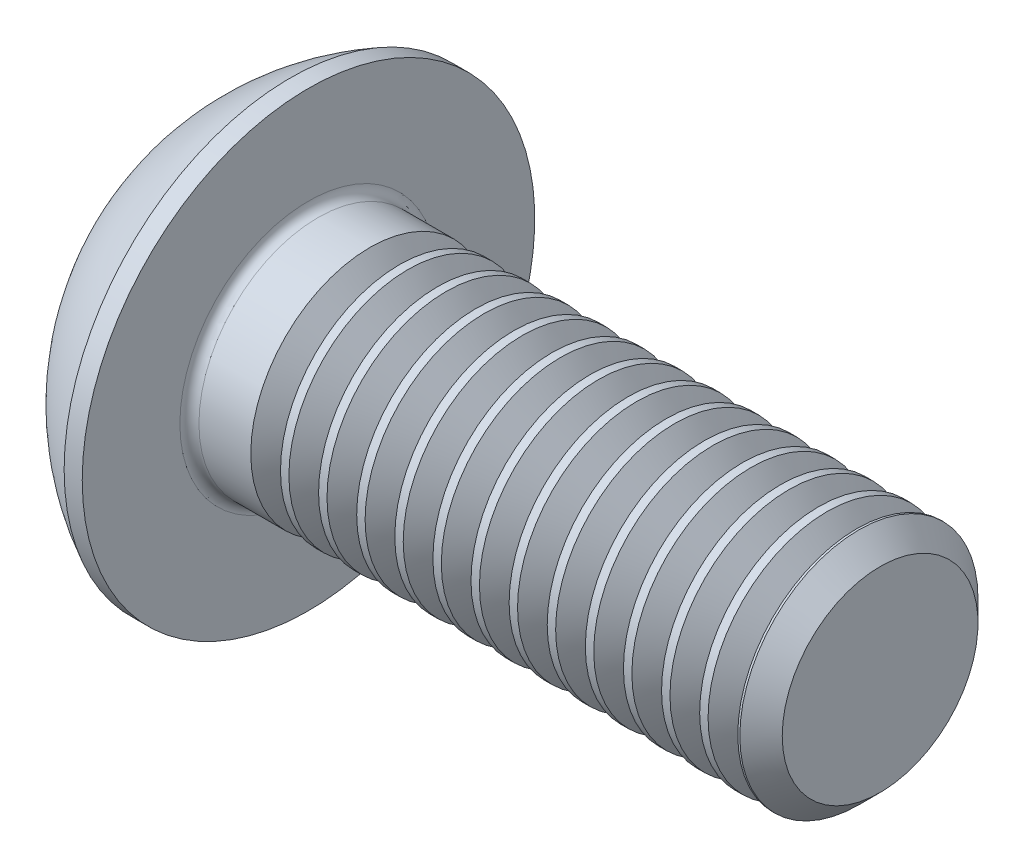
SolidWorks part; units mm, degrees
ref_plane "Plane1" through (0, 0, 0) normal (0, 0, 1) x (1, 0, 0)
ref_plane "Plane2" through (0, 0, 0) normal (0, 1, 0) x (1, 0, 0)
ref_plane "Plane3" through (0, 0, 0) normal (1, 0, 0) x (0, 0, -1)
sketch "BodySke" plane through (0, 0, 0) normal (0, 0, 1) x (1, 0, 0)
  line L0 (14.75, 0) -> (14.75, 2.055)
  line L1 (14.305, 2.5) -> (2.75, 2.5)
  line L2 (2.75, 2.5) -> (2.75, 4.75)
  line L3 (2.75, 4.75) -> (2.37, 4.75)
  line L4 (0, 0) -> (101.6, 0) construction
  line L5 (2.75, -4.75) -> (2.37, -4.75) construction
  line L6 (55.6768, -2.5) -> (2.75, -2.5) construction
  line L7 (14.75, 0) -> (0, 0)
  line L8 (0, 2.375) -> (0, -2.375) construction
  line L9 (0, 0) -> (0, 2.375)
  line L10 (14.75, 2.055) -> (14.305, 2.5)
  line L11 (14.75, -2.055) -> (14.305, -2.5) construction
  line L12 (3.55, 9.525) -> (3.55, -2.5) construction
  line L13 (2.75, 9.525) -> (2.75, -2.5) construction
  arc A1 (0, 2.375) -> (2.37, 4.75) centre (4.755, 0) cw
  dimension "D1" = 4.75
  dimension "Diameter" = 5
  dimension "Length" = 12
  dimension "Head_dia" = 9.5
  dimension "Head_ht" = 2.75
  dimension "Head_side_ht" = 0.38
  dimension "Minor_dia" = 4.11
  dimension "Body_ch_ang" = 45
  dimension "Advance" = 0.8
  dimension "Thread_nom" = 12
revolve "BaseBody" add sketch "BodySke" angle 360 about L4
cosmetic thread "ThreadCosmetic" [suppressed] parameters "Thread_length"=10.4, "Thread_minor"=4.11
fillet "Fillet1" radius 0.2 1 edges at (2.75, 0, 2.5)
sketch "Sketch2" plane through (0, 0, 0) normal (0, 0, 1) x (1, 0, 0)
  line L0 (0, 1.5) -> (1.56, 1.5)
  line L1 (1.56, 1.5) -> (2.426, 0)
  line L3 (2.426, 0) -> (0, 0)
  line L4 (0, 0) -> (0, 1.5)
  line L5 (0, -1.5) -> (1.56, -1.5) construction
  line L6 (0, 0) -> (47.625, 0) construction
  dimension "D2" = 60
  dimension "PreBroach_depth" = 1.56
  dimension "PreBroach_dia" = 3
revolve "PreBroach" cut sketch "Sketch2" angle 360 about L6
sketch "Sketch3" plane through (0, 0, 0) normal (1, 0, 0) x (0, 0, -1)
  line L0 (-1.5, -0.866) -> (-1.5, 0.866)
  line L1 (-1.5, 0.866) -> (0, 1.7321)
  line L2 (0, 1.7321) -> (1.5, 0.866)
  line L3 (1.5, 0.866) -> (1.5, -0.866)
  line L4 (1.5, -0.866) -> (0, -1.7321)
  line L5 (0, -1.7321) -> (-1.5, -0.866)
  dimension "D1" = 1.5
  dimension "D2" = 1.5
  dimension "D3" = 3
  dimension "Hex_size" = 3
extrude "Hex" cut sketch "Sketch3" along normal blind 1.56
sketch "ThdSchSke" plane through (0, 0, 0) normal (0, 0, 1) x (1, 0, 0)
  line L0 (4.35, -2.055) -> (4.0384, -2.5)
  line L1 (4.35, -2.055) -> (4.6616, -2.5)
  line L2 (4.6616, -2.5) -> (4.6616, -3.125)
  line L3 (-3.175, 0) -> (5.1513, 0) construction
  line L5 (4.6616, -3.125) -> (4.0384, -3.125)
  line L6 (4.0384, -3.125) -> (4.0384, -2.5)
  dimension "Thread_minor" = 4.11
  dimension "Diameter" = 5
  dimension "Start" = 4.35
  dimension "SideAngle" = 55
  dimension "VeeAngle" = 70
  dimension "Overcut" = 6.25
revolve "ThreadSchematic" cut sketch "ThdSchSke" angle 360 about L3
pattern_linear "ThdSchPat" count 13 spacing 0.8 along (1, 0, 0) of "ThreadSchematic"
equation "\"D1@BodySke\" = \"Head_dia@BodySke\" * .5"
equation "\"Thread_minor@ThreadCosmetic\" = \"Minor_dia@BodySke\""
equation "\"D1@Sketch3\" = \"Hex_size@Sketch3\" / 2"
equation "\"D2@Sketch3\" = \"D1@Sketch3\""
equation "\"D3@Sketch3\" = \"Hex_size@Sketch3\""
equation "\"Thread_length@ThreadCosmetic\" = ((sgn( (\"Length@BodySke\" - \"Advance@BodySke\" * 2.0) - \"Thread_nom@BodySke\" )-1)*( (\"Length@BodySke\" - \"Advance@BodySke\" * 2.0) - \"Thread_nom@BodySke\" ))/-2+ \"Thread_nom@BodySke\""
equation "\"Thread_minor@ThdSchSke\" = \"Minor_dia@BodySke\""
equation "\"Diameter@ThdSchSke\" = \"Diameter@BodySke\""
equation "\"Overcut@ThdSchSke\" = \"Diameter@BodySke\" * 1.25"
equation "\"Start@ThdSchSke\" = \"Head_ht@BodySke\" + \"Length@BodySke\" - \"Thread_length@ThreadCosmetic\"  '---Non-countersunk---"
equation "\"Num_threads@ThdSchPat\" = int( \"Thread_length@ThreadCosmetic\" / \"Advance@BodySke\" + 0.999 )  + 1"
equation "\"Advance@ThdSchPat\" = \"Thread_length@ThreadCosmetic\" /  (\"Num_threads@ThdSchPat\" - 1) 'relax it"
equation "\"Num_threads@ThdSchPat\" = \"Num_threads@ThdSchPat\" - sgn( \"Num_threads@ThdSchPat\" - 1) '---chamfered tips only---"
